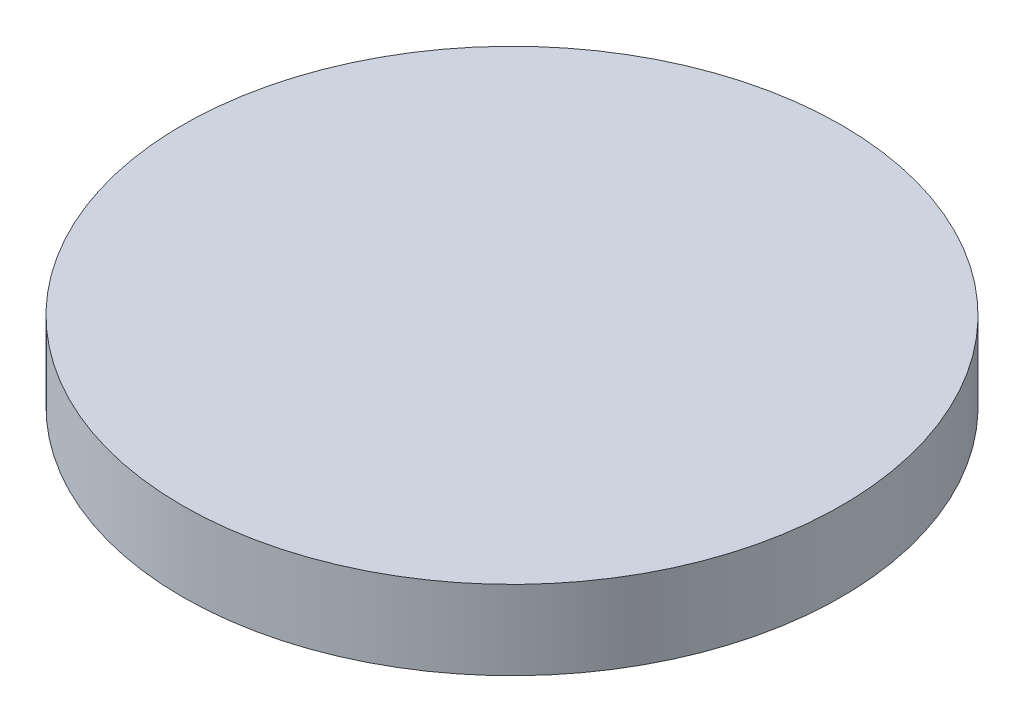
SolidWorks part; units mm, degrees
ref_plane "Front Plane" through (0, 0, 0) normal (0, 0, 1) x (1, 0, 0)
ref_plane "Top Plane" through (0, 0, 0) normal (0, 1, 0) x (1, 0, 0)
ref_plane "Right Plane" through (0, 0, 0) normal (1, 0, 0) x (0, 0, -1)
sketch "Sketch1" plane through (0, 0, 0) normal (0, 1, 0) x (1, 0, 0)
  circle A0 centre (0, 0) radius 63.5
  dimension "D1" = 127
extrude "Boss-Extrude1" add sketch "Sketch1" along normal blind 15.24
